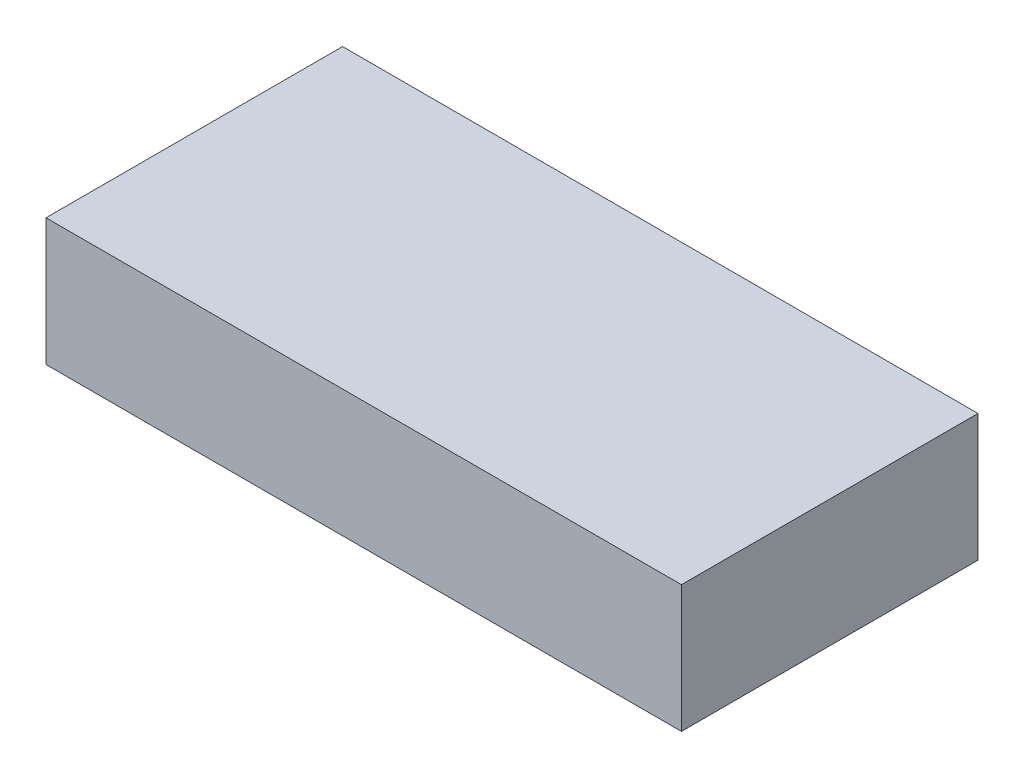
SolidWorks part; units mm, degrees
ref_plane "Front Plane" through (0, 0, 0) normal (0, 0, 1) x (1, 0, 0)
ref_plane "Top Plane" through (0, 0, 0) normal (0, 1, 0) x (1, 0, 0)
ref_plane "Right Plane" through (0, 0, 0) normal (1, 0, 0) x (0, 0, -1)
sketch "Sketch2" plane through (0, 0, 0) normal (0, 1, 0) x (1, 0, 0)
  line L1 (0, 0) -> (190.5, 0)
  line L2 (0, 0) -> (0, 88.9)
  line L3 (0, 88.9) -> (190.5, 88.9)
  line L4 (190.5, 0) -> (190.5, 88.9)
  dimension "D1" = 88.9
  dimension "D2" = 190.5
extrude "Boss-Extrude1" add sketch "Sketch2" along normal blind 38.1
